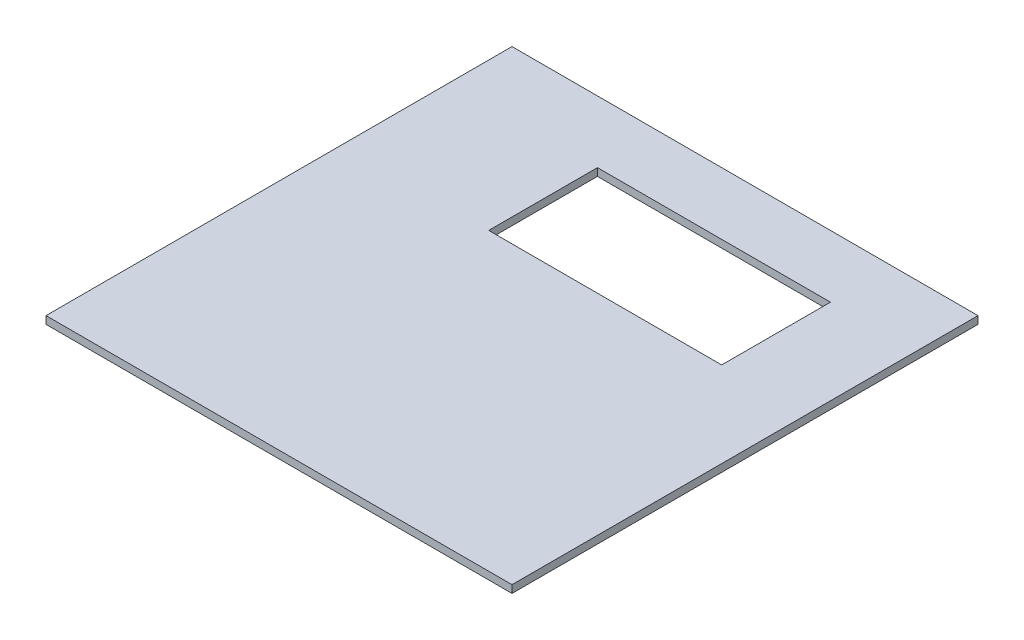
SolidWorks part; units mm, degrees
ref_plane "Front Plane" through (0, 0, 0) normal (0, 0, 1) x (1, 0, 0)
ref_plane "Top Plane" through (0, 0, 0) normal (0, 1, 0) x (1, 0, 0)
ref_plane "Right Plane" through (0, 0, 0) normal (1, 0, 0) x (0, 0, -1)
sketch "Sketch1" plane through (0, 0, 0) normal (0, 1, 0) x (1, 0, 0)
  line L1 (0, 0) -> (381, 0)
  line L2 (0, 0) -> (0, 381)
  line L3 (0, 381) -> (381, 381)
  line L4 (381, 0) -> (381, 381)
  dimension "D1" = 381
  dimension "D2" = 381
extrude "Boss-Extrude1" add sketch "Sketch1" along normal blind 6.223
sketch "Sketch4" plane through (0, 6.223, 0) normal (0, 1, 0) x (1, 0, 0)
  line L0 (381, 381) -> (0, 381) construction
  line L1 (120.65, 330.2) -> (311.15, 330.2)
  line L2 (120.65, 330.2) -> (120.65, 241.3)
  line L3 (120.65, 241.3) -> (311.15, 241.3)
  line L4 (311.15, 330.2) -> (311.15, 241.3)
  line L5 (0, 381) -> (0, 0) construction
  dimension "D1" = 190.5
  dimension "D2" = 88.9
  dimension "D3" = 50.8
  dimension "D4" = 120.65
extrude "Cut-Extrude1" cut sketch "Sketch4" against normal blind 203.2 contours L3 L4 L1 L2
